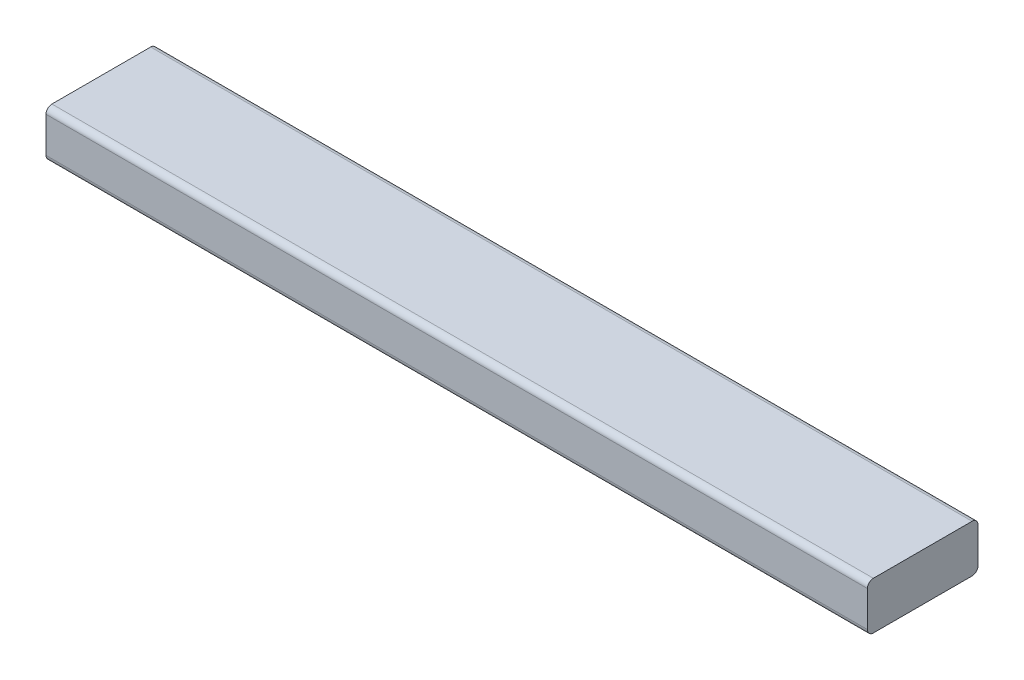
SolidWorks part; units mm, degrees
material "Pine"
ref_plane "Front Plane" through (0, 0, 0) normal (0, 0, 1) x (1, 0, 0)
ref_plane "Top Plane" through (0, 0, 0) normal (0, 1, 0) x (1, 0, 0)
ref_plane "Right Plane" through (0, 0, 0) normal (1, 0, 0) x (0, 0, -1)
sketch "Sketch1" plane through (0, 0, 0) normal (0, 1, 0) x (1, 0, 0)
  line L1 (-330.2, -44.45) -> (330.2, -44.45)
  line L2 (-330.2, -44.45) -> (-330.2, 44.45)
  line L3 (-330.2, 44.45) -> (330.2, 44.45)
  line L4 (330.2, -44.45) -> (330.2, 44.45)
  line L5 (-330.2, -44.45) -> (330.2, 44.45) construction
  line L6 (-330.2, 44.45) -> (330.2, -44.45) construction
  point P0 (0, 0)
  dimension "D1" = 660.4
  dimension "D2" = 88.9
extrude "Boss-Extrude1" add sketch "Sketch1" along normal blind 38.1
fillet "Fillet1" radius 4.7625 4 edges at (0, 0, -44.45) (0, 38.1, -44.45) (0, 0, 44.45) (0, 38.1, 44.45)
